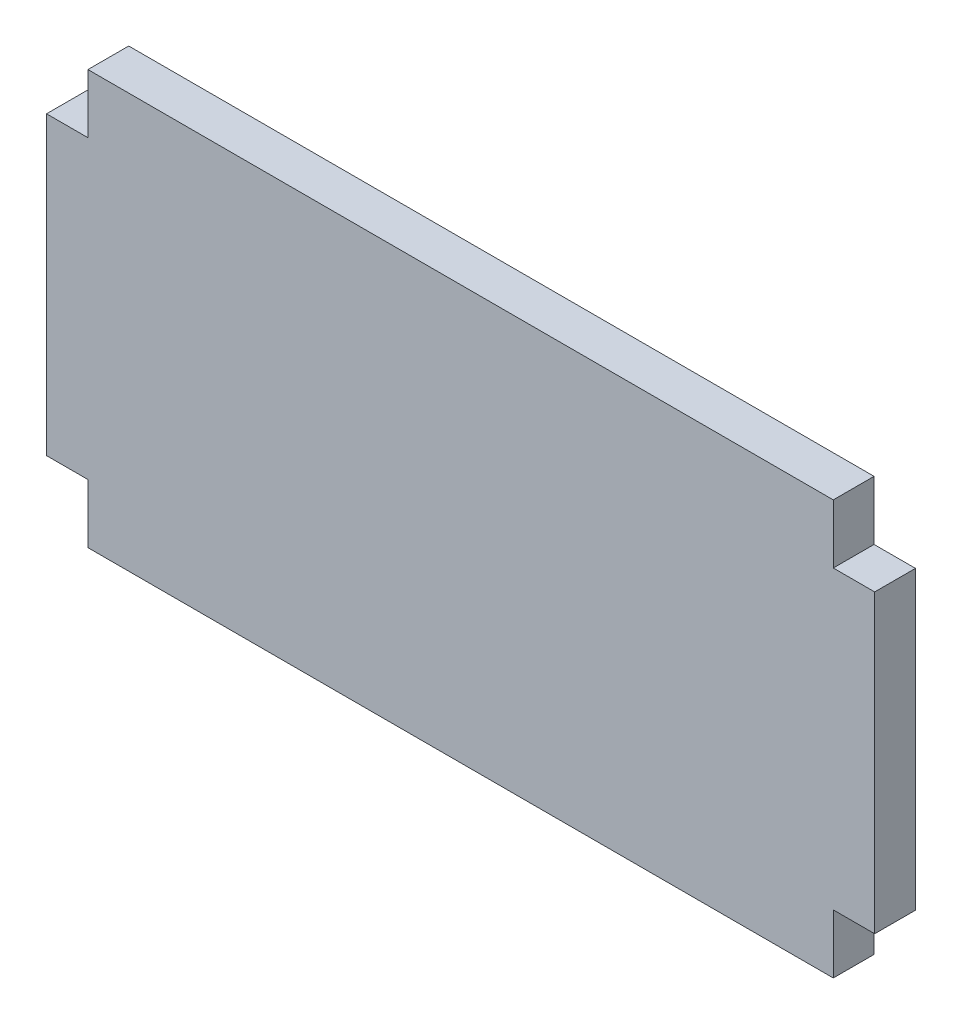
SolidWorks part; units mm, degrees
material "Pine"
ref_plane "Front Plane" through (0, 0, 0) normal (0, 0, 1) x (1, 0, 0)
ref_plane "Top Plane" through (0, 0, 0) normal (0, 1, 0) x (1, 0, 0)
ref_plane "Right Plane" through (0, 0, 0) normal (1, 0, 0) x (0, 0, -1)
sketch "Sketch1" plane through (0, 0, 0) normal (0, 0, 1) x (1, 0, 0)
  line L0 (-45.72, 25.4) -> (-45.72, 18.161)
  line L1 (45.72, 25.4) -> (-45.72, 25.4)
  line L2 (50.8, 18.161) -> (50.8, -18.161)
  line L3 (45.72, -25.4) -> (-45.72, -25.4)
  line L4 (-50.8, 18.161) -> (-50.8, -18.161)
  line L5 (0, 0) -> (0, 18.161) construction
  line L7 (-45.72, 18.161) -> (-50.8, 18.161)
  line L11 (0, 0) -> (-25.2212, 0) construction
  line L12 (45.72, 25.4) -> (45.72, 18.161)
  line L13 (45.72, 18.161) -> (50.8, 18.161)
  line L14 (45.72, -18.161) -> (50.8, -18.161)
  line L15 (45.72, -25.4) -> (45.72, -18.161)
  line L16 (-45.72, -25.4) -> (-45.72, -18.161)
  line L17 (-45.72, -18.161) -> (-50.8, -18.161)
  point P0 (0, 0)
  point P1 (-50.8, -25.4)
  point P2 (50.8, 25.4)
  point P4 (-50.8, 25.4)
  point P7 (-45.72, -25.4)
  point P8 (50.8, 18.161)
extrude "Boss-Extrude1" add sketch "Sketch1" along normal blind 5.0038
